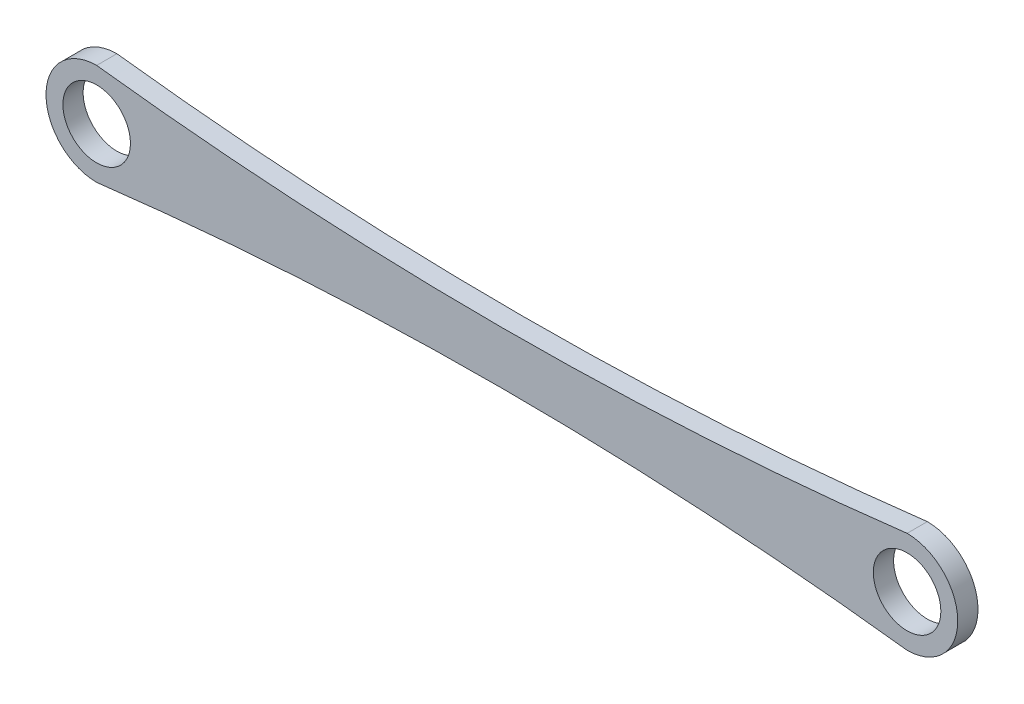
SolidWorks part; units mm, degrees
ref_plane "Front Plane" through (0, 0, 0) normal (0, 0, 1) x (1, 0, 0)
ref_plane "Top Plane" through (0, 0, 0) normal (0, 1, 0) x (1, 0, 0)
ref_plane "Right Plane" through (0, 0, 0) normal (1, 0, 0) x (0, 0, -1)
sketch "Sketch1" plane through (0, 0, 0) normal (0, 0, 1) x (1, 0, 0)
  line L0 (0, 0) -> (120, 0) construction
  line L1 (0, 0) -> (120, 0) construction
  line L2 (0, 7.5) -> (120, 7.5)
  line L3 (0, -7.5) -> (120, -7.5)
  circle A0 centre (0, 0) radius 5
  circle A1 centre (120, 0) radius 5
  arc A2 (0, 7.5) -> (0, -7.5) centre (0, 0) ccw
  arc A3 (120, -7.5) -> (120, 7.5) centre (120, 0) ccw
  arc A4 (0, 7.5) -> (120, 7.5) centre (60, 503.8869) ccw
  arc A5 (0, -7.5) -> (120, -7.5) centre (60, -503.8869) cw
  point P5 (60, 0)
  dimension "D2" = 10
  dimension "D4" = 500
  dimension "D5" = 500
  dimension "D1" = 120
  dimension "D3" = 15
extrude "Boss-Extrude1" add sketch "Sketch1" along normal blind 3 contours A2 A5 A3 A4 A0 A1
